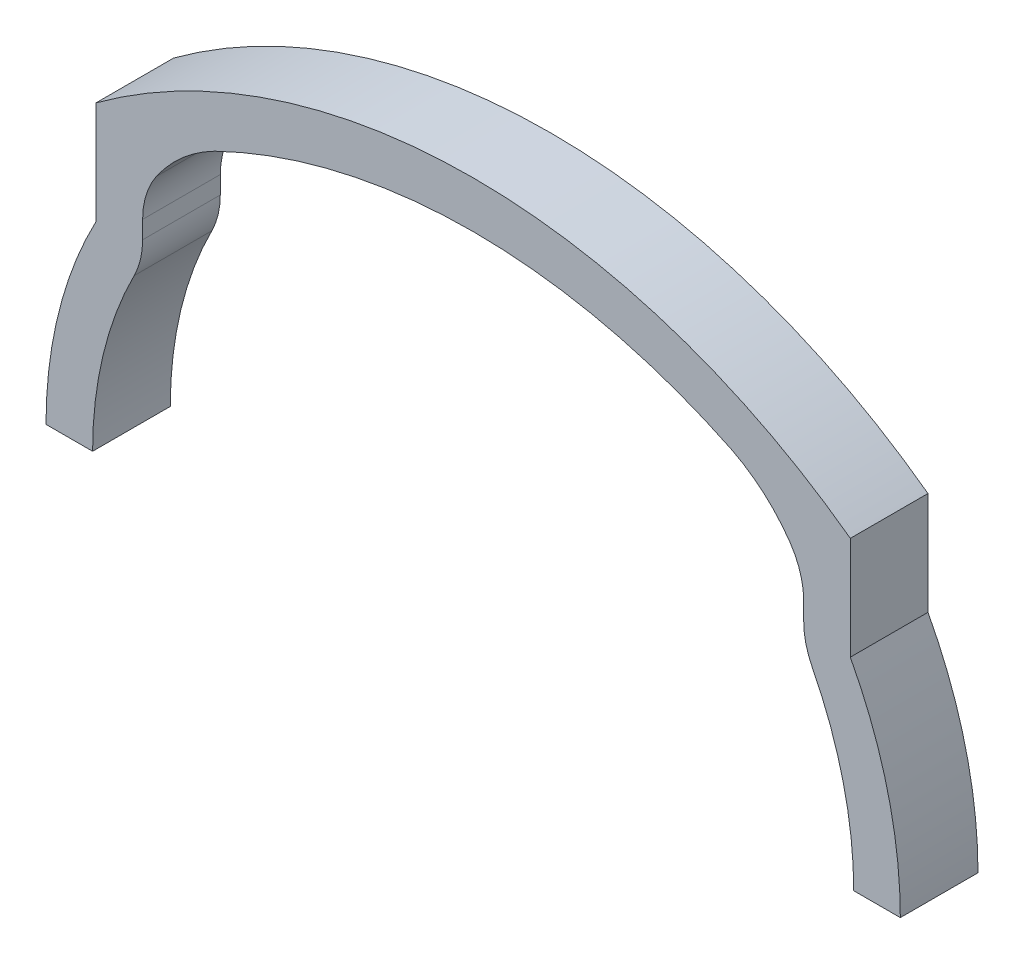
SolidWorks part; units mm, degrees
ref_plane "Front Plane" through (0, 0, 0) normal (0, 0, 1) x (1, 0, 0)
ref_plane "Top Plane" through (0, 0, 0) normal (0, 1, 0) x (1, 0, 0)
ref_plane "Right Plane" through (0, 0, 0) normal (1, 0, 0) x (0, 0, -1)
sketch "Sketch1" plane through (0, 0, 0) normal (0, 0, 1) x (1, 0, 0)
  line L1 (67.3394, 0) -> (0, 0) construction
  line L2 (0, 0) -> (0, 65.2519) construction
  line L4 (-21, 17.5685) -> (-19.0192, 14.638) construction
  line L5 (21, 17.5685) -> (19.0192, 14.638) construction
  line L6 (-24.5, 0) -> (24.5, 0)
  line L8 (-21.28, 14.5401) -> (-21.28, 13.4019)
  line L9 (21.28, 14.5401) -> (21.28, 13.4019)
  line L12 (24.28, 19.5376) -> (24.28, 12.9125)
  line L13 (-24.28, 19.5376) -> (-24.28, 12.9125)
  line L14 (-27.5, 0) -> (27.5, 0)
  line L15 (-21.28, 17.9827) -> (-21.28, 12.1413) construction
  line L16 (21.28, 17.9827) -> (21.28, 12.1413) construction
  line L17 (-27.3359, -3) -> (27.3359, -3) construction
  arc A2 (21, 17.5685) -> (-21, 17.5685) centre (0, -13.5) ccw construction
  arc A4 (24.5, 0) -> (21.8258, 11.1304) centre (0, 0) ccw
  arc A6 (16.6444, 20.6609) -> (-16.6444, 20.6609) centre (0, -13.5) ccw
  arc A8 (-21.8258, 11.1304) -> (-24.5, 0) centre (0, 0) ccw
  arc A9 (24.5, 0) -> (-24.5, 0) centre (0, 0) ccw construction
  arc A10 (24, 0) -> (-24, 0) centre (0, 0) ccw construction
  arc A11 (27.5, 0) -> (24.28, 12.9125) centre (0, 0) ccw
  arc A12 (24.28, 19.5376) -> (-24.28, 19.5376) centre (0, -13.5) ccw
  arc A13 (-24.28, 12.9125) -> (-27.5, 0) centre (0, 0) ccw
  arc A14 (-24.28, 12.9125) -> (-27.3359, -3) centre (0, 0) ccw construction
  arc A15 (27.3359, -3) -> (24.28, 12.9125) centre (0, 0) ccw construction
  arc A18 (21.28, 17.9827) -> (-21.28, 17.9827) centre (0, -13.5) ccw construction
  arc A19 (-16.6444, 20.6609) -> (-20.3928, 17.3836) centre (-12.0318, 11.6031) ccw
  arc A20 (16.6444, 20.6609) -> (20.3928, 17.3836) centre (12.0318, 11.6031) cw
  arc A21 (24.5, 0) -> (21.28, 12.1413) centre (0, 0) ccw construction
  arc A22 (21.28, 13.4019) -> (21.8258, 11.1304) centre (26.28, 13.4019) ccw
  arc A23 (20.3928, 17.3836) -> (21.28, 14.5401) centre (16.28, 14.5401) cw
  arc A24 (-21.28, 12.1413) -> (-24.5, 0) centre (0, 0) ccw construction
  arc A25 (-21.28, 13.4019) -> (-21.8258, 11.1304) centre (-26.28, 13.4019) cw
  arc A26 (-20.3928, 17.3836) -> (-21.28, 14.5401) centre (-16.28, 14.5401) ccw
  point P4 (0, 24)
  point P5 (0, 24)
  point P44 (21.28, 15.821)
  point P50 (-21.28, 15.821)
  dimension "D1" = 24
  dimension "D2" = 75
  dimension "D6" = 5
  dimension "D3" = 42
  dimension "D4" = 0.5
  dimension "D5" = 3
extrude "Boss-Extrude3" add sketch "Sketch1" along normal blind 5 contours A6 A20 L9 A4 L14 A11 L12 A12 L13 A13 A8 L8 A19
